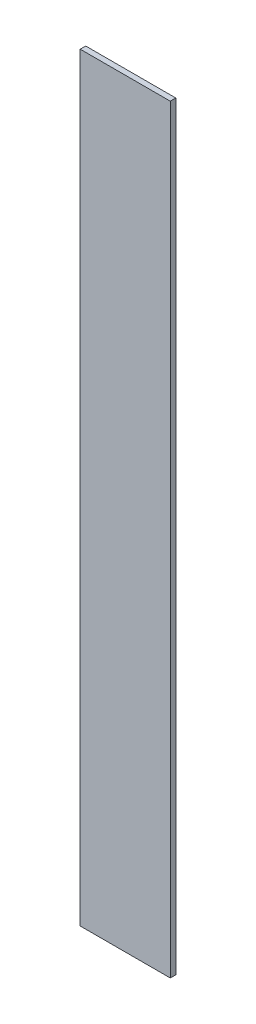
SolidWorks part; units mm, degrees
ref_plane "Front Plane" through (0, 0, 0) normal (0, 0, 1) x (1, 0, 0)
ref_plane "Top Plane" through (0, 0, 0) normal (0, 1, 0) x (1, 0, 0)
ref_plane "Right Plane" through (0, 0, 0) normal (1, 0, 0) x (0, 0, -1)
sketch "Sketch1" plane through (0, 0, 0) normal (0, 1, 0) x (1, 0, 0)
  line L0 (29.8232, 55.805) -> (29.6257, 52.8115) construction
  line L1 (-52.0023, 55.805) -> (29.8232, 55.805)
  line L2 (-52.0023, 55.805) -> (-52.0023, 50.805)
  line L3 (-52.0023, 50.805) -> (29.8232, 50.805)
  line L4 (29.8232, 55.805) -> (29.8232, 50.805)
  line L5 (-21.3075, -59.2094) -> (-69.6505, 114.0583) construction
  dimension "D2" = 5
extrude "Boss-Extrude1" add sketch "Sketch1" along normal blind 690.01
